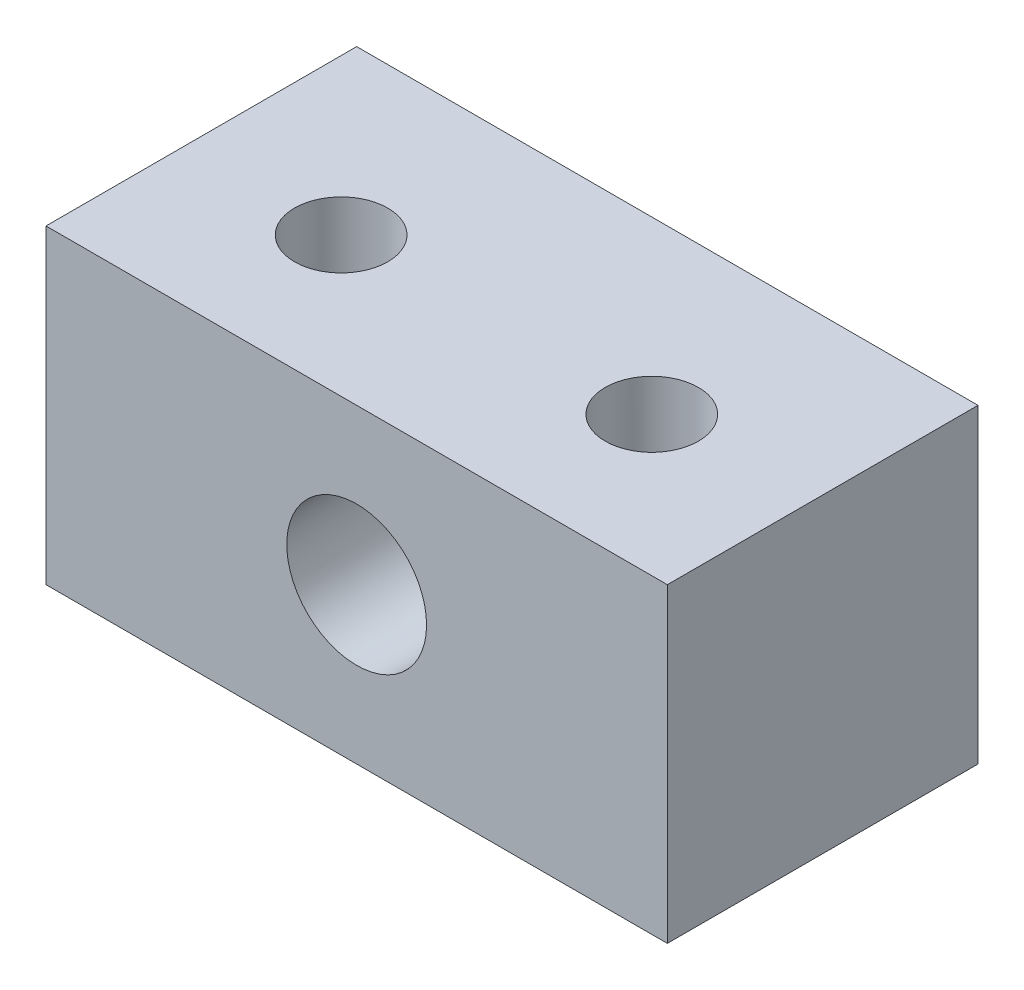
SolidWorks part; units mm, degrees
ref_plane "Front Plane" through (0, 0, 0) normal (0, 0, 1) x (1, 0, 0)
ref_plane "Top Plane" through (0, 0, 0) normal (0, 1, 0) x (1, 0, 0)
ref_plane "Right Plane" through (0, 0, 0) normal (1, 0, 0) x (0, 0, -1)
sketch "Esquisse1" plane through (0, 0, 0) normal (0, 0, 1) x (1, 0, 0)
  line L1 (0, 10) -> (20, 10)
  line L2 (0, 10) -> (0, 0)
  line L3 (0, 0) -> (20, 0)
  line L4 (20, 10) -> (20, 0)
  dimension "D1" = 10
  dimension "D2" = 20
extrude "Boss.-Extru.1" add sketch "Esquisse1" along normal blind 10
sketch "Esquisse2" plane through (0, 0, 10) normal (0, 0, 1) x (1, 0, 0)
  line L0 (0, 10) -> (0, 0) construction
  line L1 (20, 10) -> (0, 10) construction
  circle A0 centre (10, 5) radius 2.25
  point P5 (0, 5)
  point P8 (10, 10)
  dimension "D1" = 4.5
extrude "Enlèv. mat.-Extru.1" cut sketch "Esquisse2" against normal through all
sketch "Esquisse3" plane through (0, 10, 0) normal (0, 1, 0) x (1, 0, 0)
  line L0 (0, -10) -> (0, 0) construction
  line L1 (20, -10) -> (0, -10) construction
  line L2 (20, -10) -> (20, 0) construction
  circle A0 centre (5, -5.5) radius 1.5
  circle A1 centre (15, -5.5) radius 1.5
  dimension "D1" = 3
  dimension "D2" = 5
  dimension "D3" = 4.5
  dimension "D4" = 5
extrude "Enlèv. mat.-Extru.2" cut sketch "Esquisse3" against normal through all and the other way through all
